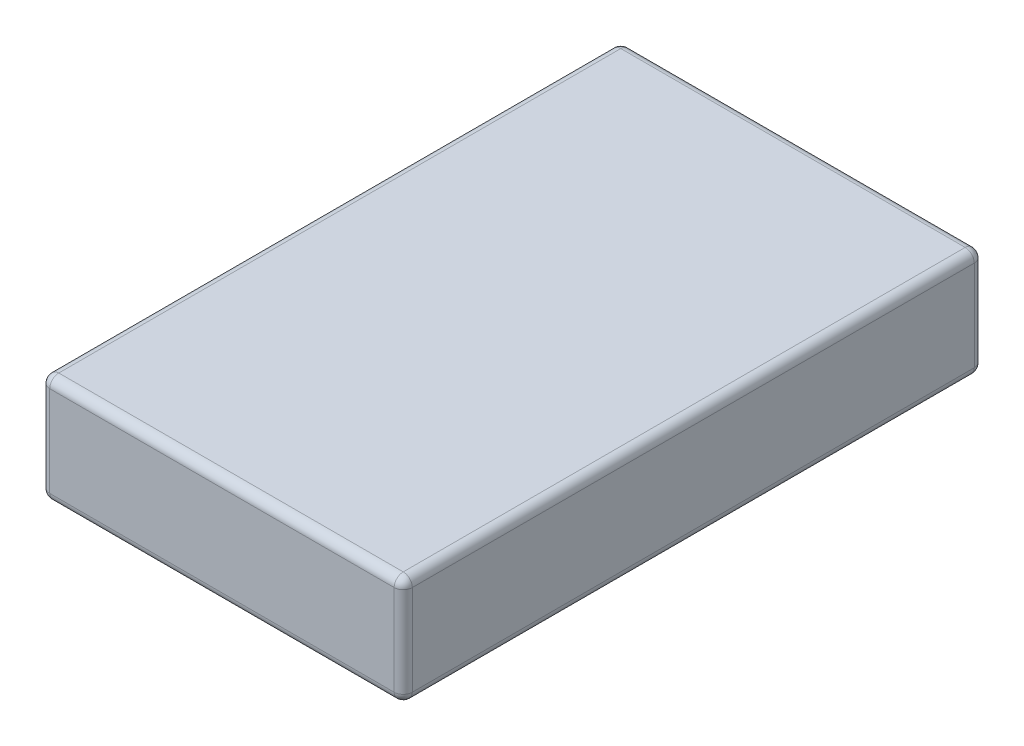
SolidWorks part; units mm, degrees
ref_plane "Front Plane" through (0, 0, 0) normal (0, 0, 1) x (1, 0, 0)
ref_plane "Top Plane" through (0, 0, 0) normal (0, 1, 0) x (1, 0, 0)
ref_plane "Right Plane" through (0, 0, 0) normal (1, 0, 0) x (0, 0, -1)
sketch "Sketch1" plane through (0, 0, 0) normal (0, 1, 0) x (1, 0, 0)
  line L1 (-10, -16) -> (10, -16)
  line L2 (-10, -16) -> (-10, 16)
  line L3 (-10, 16) -> (10, 16)
  line L4 (10, -16) -> (10, 16)
  line L5 (-10, -16) -> (10, 16) construction
  line L6 (-10, 16) -> (10, -16) construction
  point P0 (0, 0)
  dimension "D1" = 20
  dimension "D2" = 32
extrude "Boss-Extrude1" add sketch "Sketch1" along normal blind 6
fillet "Fillet1" radius 0.5 12 edges at (-10, 3, -16) (-10, 3, 16) (10, 3, 16) (10, 3, -16) (0, 0, -16) (-10, 0, 0) (0, 0, 16) (10, 0, 0) (0, 6, 16) (-10, 6, 0) (0, 6, -16) (10, 6, 0)
